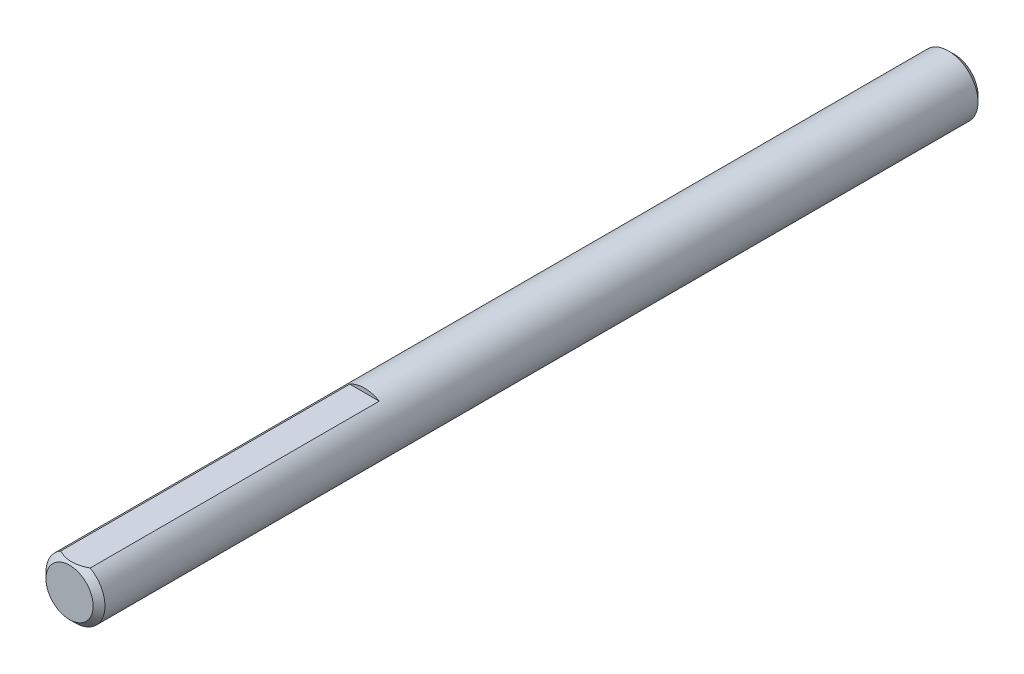
SolidWorks part; units mm, degrees
ref_plane "Front" through (0, 0, 0) normal (0, 0, 1) x (1, 0, 0)
ref_plane "Top" through (0, 0, 0) normal (0, 1, 0) x (1, 0, 0)
ref_plane "Right" through (0, 0, 0) normal (1, 0, 0) x (0, 0, -1)
sketch "Sketch1" plane through (0, 0, 0) normal (0, 0, 1) x (1, 0, 0)
  circle A0 centre (0, 0) radius 2.54
  dimension "D1" = 5.08
extrude "Extrude1" add sketch "Sketch1" along normal mid plane 76.2
chamfer "Chamfer1" distance 0.508 angle 45 2 edges at (2.54, 0, -38.1) (2.54, 0, 38.1)
ref_plane "Plane1" through (0, 0, 12.7) normal (0, 0, 1) x (1, 0, 0)
sketch "Sketch13" plane through (0, 0, 12.7) normal (0, 0, 1) x (1, 0, 0)
  line L3 (-1.27, 2.1997) -> (1.27, 2.1997)
  circle A0 centre (0, 0) radius 2.54 construction
  arc A1 (1.27, 2.1997) -> (-1.27, 2.1997) centre (0, 0) ccw
  dimension "D1" = 2.54
extrude "Extrude7" cut sketch "Sketch13" along normal through all
equation "\"D1@Chamfer1\" = \"D1@Sketch1\" * .1"
equation "\"D1@Sketch13\" = \"D1@Sketch1\" * .5"
